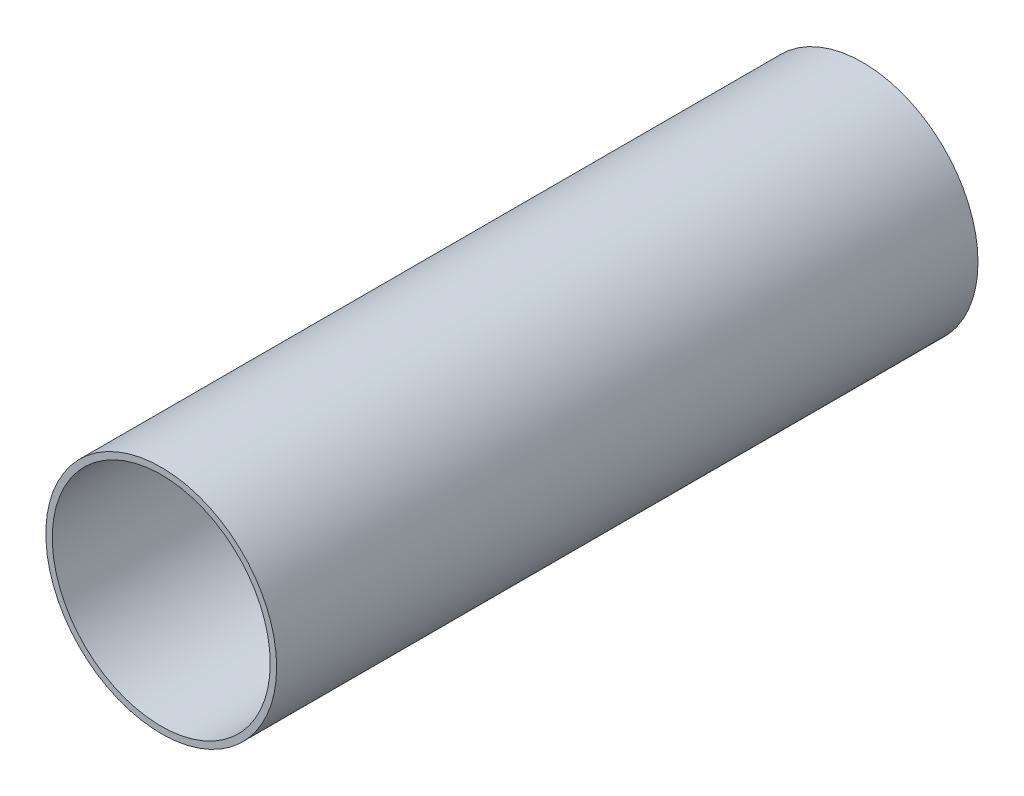
SolidWorks part; units mm, degrees
material "Rubber"
ref_plane "Front Plane" through (0, 0, 0) normal (0, 0, 1) x (1, 0, 0)
ref_plane "Top Plane" through (0, 0, 0) normal (0, 1, 0) x (1, 0, 0)
ref_plane "Right Plane" through (0, 0, 0) normal (1, 0, 0) x (0, 0, -1)
sketch "Sketch1" plane through (0, 0, 0) normal (0, 0, 1) x (1, 0, 0)
  circle A0 centre (0, 0) radius 2.25
  circle A1 centre (0, 0) radius 2.125
  dimension "D1" = 4.5
  dimension "D2" = 4.25
extrude "Boss-Extrude1" add sketch "Sketch1" along normal blind 13.675
equation "\"D2@Sketch1\"=4.5-0.25"
